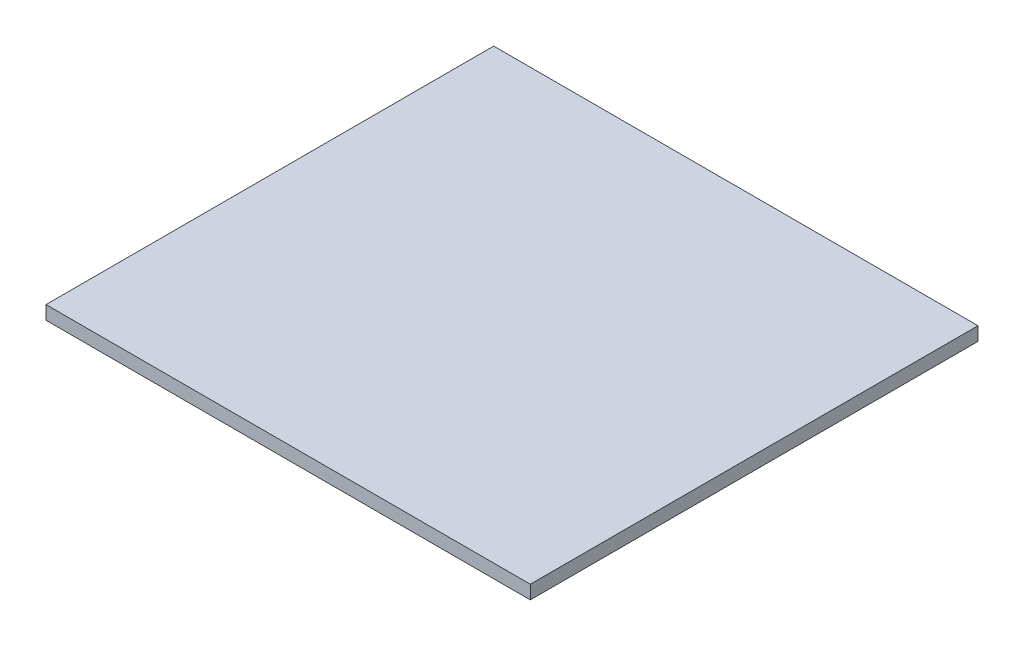
SolidWorks part; units mm, degrees
ref_plane "Front Plane" through (0, 0, 0) normal (0, 0, 1) x (1, 0, 0)
ref_plane "Top Plane" through (0, 0, 0) normal (0, 1, 0) x (1, 0, 0)
ref_plane "Right Plane" through (0, 0, 0) normal (1, 0, 0) x (0, 0, -1)
sketch "Sketch1" plane through (0, 0, 0) normal (0, 1, 0) x (1, 0, 0)
  line L1 (-44.2815, 20.698) -> (62.5985, 20.698)
  line L2 (-44.2815, 20.698) -> (-44.2815, -78.102)
  line L3 (-44.2815, -78.102) -> (62.5985, -78.102)
  line L4 (62.5985, 20.698) -> (62.5985, -78.102)
  dimension "D1" = 106.88
  dimension "D2" = 98.8
extrude "Boss-Extrude1" add sketch "Sketch1" along normal blind 3
equation "\"Fit\"= 1"
equation "\"cover width\"= 98.8"
equation "\"bottom 6 length\"= 106.88"
equation "\"thinner acrylic\"= 3"
equation "\"D1@Sketch1\"=\"bottom 6 length\""
equation "\"D2@Sketch1\"=\"cover width\""
equation "\"D1@Boss-Extrude1\"=\"thinner acrylic\""
